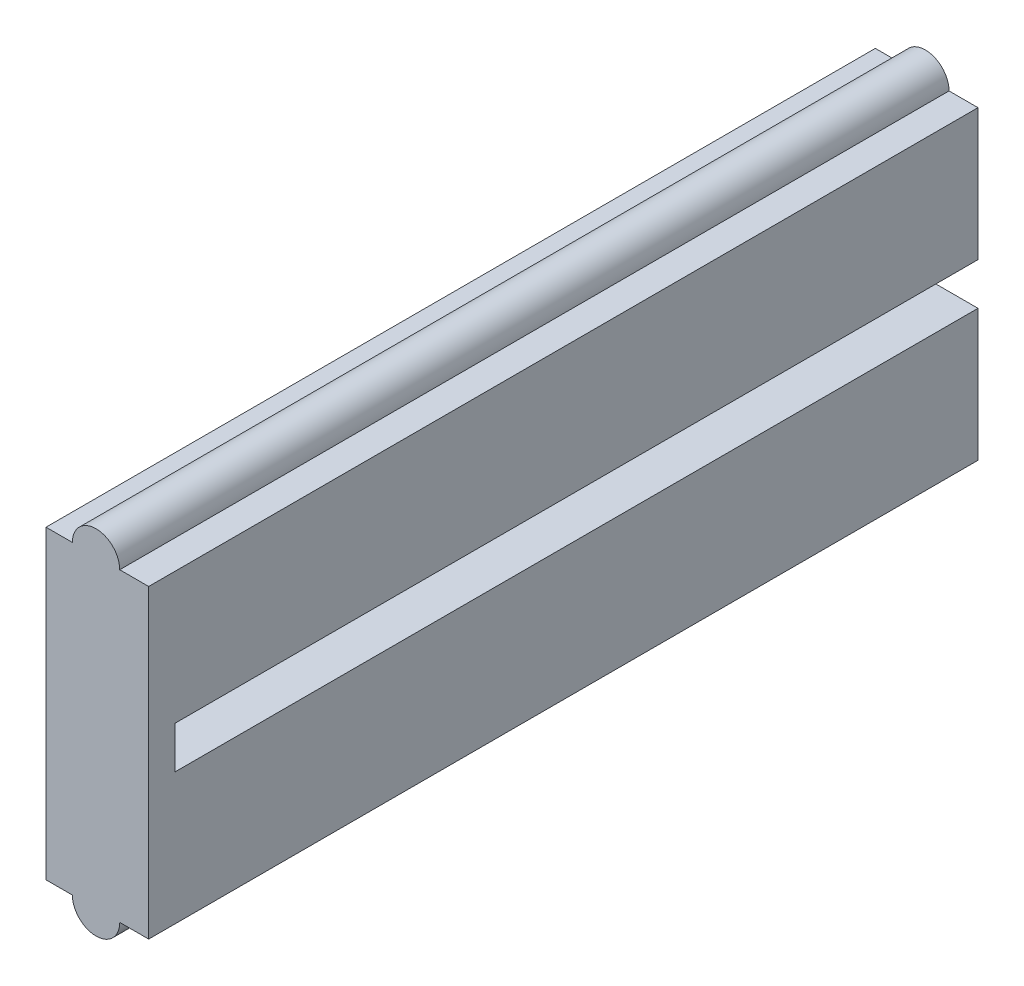
SolidWorks part; units mm, degrees
ref_plane "Front Plane" through (0, 0, 0) normal (0, 0, 1) x (1, 0, 0)
ref_plane "Top Plane" through (0, 0, 0) normal (0, 1, 0) x (1, 0, 0)
ref_plane "Right Plane" through (0, 0, 0) normal (1, 0, 0) x (0, 0, -1)
sketch "Sketch1" plane through (0, 0, 0) normal (0, 0, 1) x (1, 0, 0)
  line L0 (0, 5.2525) -> (0, -5.3788) construction
  line L1 (-1.9, 5.8) -> (-0.9, 5.8)
  line L2 (-1.9, 5.8) -> (-1.9, -5.8)
  line L3 (-1.9, -5.8) -> (-0.898, -5.8)
  line L4 (2, 5.8) -> (2, 0.8)
  line L5 (-6.2626, 0) -> (8.4343, 0) construction
  line L7 (2, 0.8) -> (0, 0.8)
  line L9 (2, -0.8) -> (0, -0.8)
  line L15 (2, -0.8) -> (2, -5.8)
  line L16 (0.9, 5.8) -> (2, 5.8)
  line L17 (0.902, -5.8) -> (2, -5.8)
  line L18 (0, 0.8) -> (0, -0.8)
  arc A0 (-0.9, 5.8) -> (0.9, 5.8) centre (0, 5.8) cw
  arc A1 (0.902, -5.8) -> (-0.898, -5.8) centre (0.002, -5.8) cw
  point P13 (0, 0)
  point P14 (0, 0)
  point P15 (0, 0)
  point P16 (0, 0)
  point P23 (0, 0)
  dimension "D6" = 0.9
  dimension "D8" = 0.9
  dimension "D1" = 2
  dimension "D2" = 11.6
  dimension "D3" = 1.9
  dimension "D4" = 2
  dimension "D5" = 0
  dimension "D7" = 1.6
  dimension "D9" = 0
  dimension "D10" = 2
extrude "Boss-Extrude1" add sketch "Sketch1" along normal blind 31.5
sketch "Sketch2" plane through (0, 0, 0) normal (0, 0, -1) x (-1, 0, 0)
  line L1 (-2, 0.8) -> (0, 0.8)
  line L2 (-2, 0.8) -> (-2, -0.8)
  line L3 (-2, -0.8) -> (0, -0.8)
  line L4 (0, 0.8) -> (0, -0.8)
extrude "Boss-Extrude2" add sketch "Sketch2" along normal blind 1 from surface at -31.5 starting at face at (0.3503, 0, 31.5)
